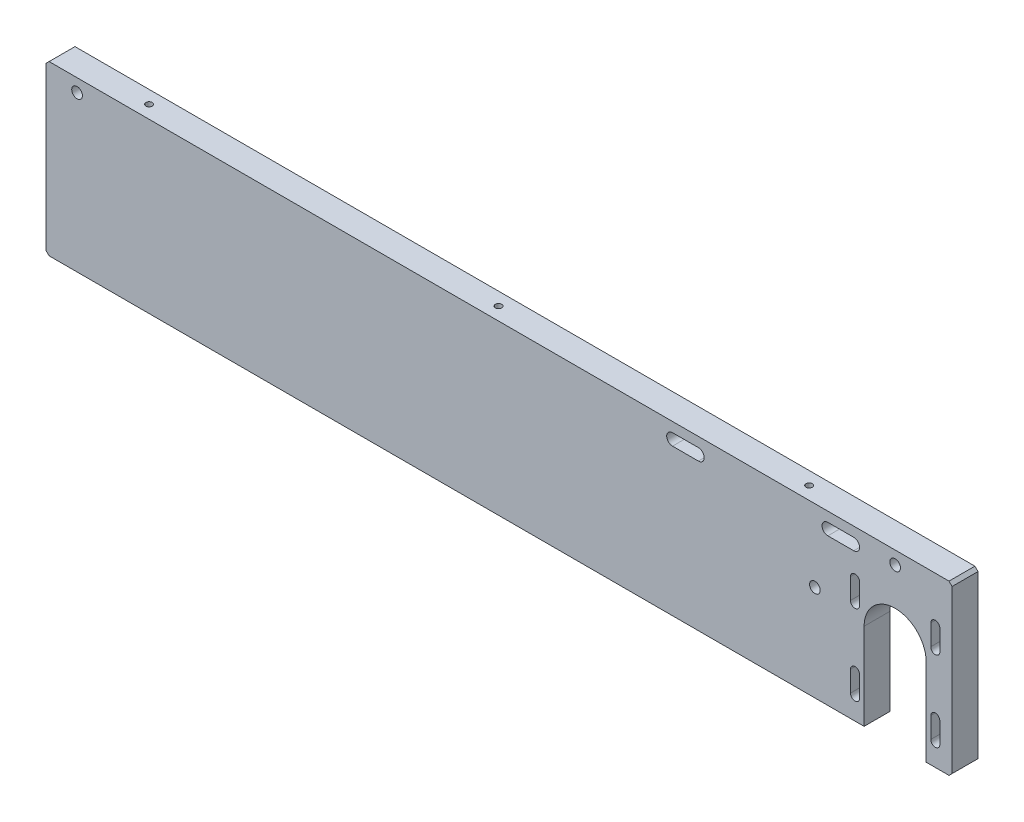
SolidWorks part; units mm, degrees
ref_plane "Front Plane" through (0, 0, 0) normal (0, 0, 1) x (1, 0, 0)
ref_plane "Top Plane" through (0, 0, 0) normal (0, 1, 0) x (1, 0, 0)
ref_plane "Right Plane" through (0, 0, 0) normal (1, 0, 0) x (0, 0, -1)
sketch "Sketch1" plane through (0, 0, 0) normal (0, 0, 1) x (1, 0, 0)
  line L0 (348.8, 65) -> (350, 63.8)
  line L1 (1.2, 0) -> (348.8, 0)
  line L2 (0, 1.2) -> (0, 63.8)
  line L3 (1.2, 65) -> (348.8, 65)
  line L4 (350, 1.2) -> (350, 63.8)
  line L5 (348.8, 0) -> (350, 1.2)
  line L6 (0, 1.2) -> (1.2, 0)
  line L7 (0, 63.8) -> (1.2, 65)
  point P0 (0, 0)
  point P1 (350, 65)
  point P2 (0, 65)
  point P3 (350, 0)
  dimension "D1" = 350
  dimension "D2" = 65
extrude "Boss-Extrude1" add sketch "Sketch1" along normal blind 10 contours L3 L0 L4 L5 L1 L6 L2 L7
sketch "Sketch2" plane through (0, 0, 10) normal (0, 0, 1) x (1, 0, 0)
  line L0 (316, 0) -> (316, 33.5)
  line L1 (1.2, 0) -> (348.8, 0) construction
  line L2 (340, 33.5) -> (340, 0)
  line L3 (350, 1.2) -> (350, 63.8) construction
  line L4 (316, 0) -> (340, 0)
  arc A0 (316, 33.5) -> (340, 33.5) centre (328, 33.5) cw
  point P0 (316, 0)
  point P8 (340, 0)
  line M7 (1.2, 0) -> (348.8, 0)
  dimension "D2" = 12
  dimension "D1" = 33.5
  dimension "D3" = 10
  dimension "D4" = 24
extrude "Cut-Extrude1" cut sketch "Sketch2" against normal through all and the other way through all contours A0 L0 L2 M7
sketch "Sketch3" plane through (0, 0, 10) normal (0, 0, 1) x (1, 0, 0)
  line L0 (343.5, 16.5) -> (343.5, 8.5) construction
  line L1 (345.25, 16.5) -> (345.25, 8.5)
  line L2 (341.75, 16.5) -> (341.75, 8.5)
  line L3 (340, 0) -> (348.8, 0) construction
  line L5 (350, 1.2) -> (350, 63.8) construction
  arc A0 (345.25, 16.5) -> (341.75, 16.5) centre (343.5, 16.5) ccw
  arc A1 (341.75, 8.5) -> (345.25, 8.5) centre (343.5, 8.5) ccw
  point P2 (343.5, 12.5)
  dimension "D1" = 1.75
  dimension "D4" = 4.75
  dimension "D2" = 8
  dimension "D3" = 8.5
extrude "Cut-Extrude2" cut sketch "Sketch3" against normal through all
pattern_linear "LPattern1" count 2 spacing 31 along (0, 1, 0) count 2 spacing 31 along (-1, 0, 0) of "Cut-Extrude2"
sketch "Sketch5" plane through (0, 0, 10) normal (0, 0, 1) x (1, 0, 0)
  line L0 (302, 59) -> (312, 59) construction
  line L1 (302, 61.25) -> (312, 61.25)
  line L2 (302, 56.75) -> (312, 56.75)
  line L3 (242, 59) -> (252, 59) construction
  line L4 (242, 61.25) -> (252, 61.25)
  line L5 (242, 56.75) -> (252, 56.75)
  line L6 (350, 1.2) -> (350, 63.8) construction
  line L7 (1.2, 65) -> (348.8, 65) construction
  line L8 (0, 1.2) -> (0, 63.8) construction
  circle A0 centre (328, 60) radius 2.065
  arc A1 (302, 61.25) -> (302, 56.75) centre (302, 59) ccw
  arc A2 (312, 56.75) -> (312, 61.25) centre (312, 59) ccw
  arc A3 (242, 61.25) -> (242, 56.75) centre (242, 59) ccw
  arc A4 (252, 56.75) -> (252, 61.25) centre (252, 59) ccw
  circle A5 centre (12, 60) radius 2.065
  circle A6 centre (297, 37) radius 2.065
  arc A8 (310.75, 39.5) -> (314.25, 39.5) centre (312.5, 39.5) ccw construction
  point P4 (307, 59)
  point P9 (247, 59)
  dimension "D1" = 4.13
  dimension "D2" = 22
  dimension "D3" = 5
  dimension "D5" = 2.25
  dimension "D7" = 38
  dimension "D8" = 50
  dimension "D9" = 4.13
  dimension "D10" = 12
  dimension "D11" = 15.5
  dimension "D13" = 4.13
  dimension "D4" = 10
  dimension "D6" = 3.75
  dimension "D12" = 28
extrude "Cut-Extrude3" cut sketch "Sketch5" against normal through all
sketch "Sketch6" plane through (0, 65, 0) normal (0, 1, 0) x (1, 0, 0)
  line L0 (348.8, -10) -> (348.8, 0) construction
  circle A0 centre (289.8, -5) radius 1.23
  circle A1 centre (169.8, -5) radius 1.23
  circle A2 centre (34.8, -5) radius 1.23
  point P8 (348.8, -5)
  point P9 (0, 0)
  dimension "D1" = 2.46
  dimension "D2" = 59
  dimension "D3" = 120
  dimension "D4" = 135
extrude "Cut-Extrude4" cut sketch "Sketch6" against normal blind 8
